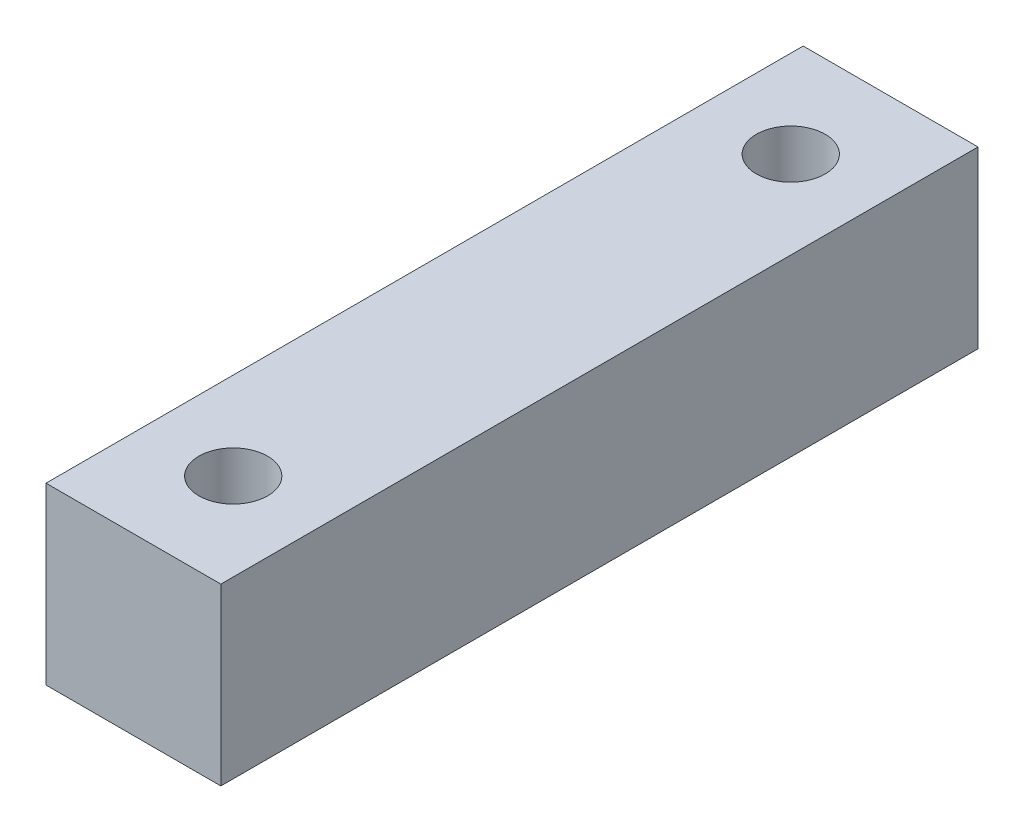
SolidWorks part; units mm, degrees
ref_plane "Front" through (0, 0, 0) normal (0, 0, 1) x (1, 0, 0)
ref_plane "Top" through (0, 0, 0) normal (0, 1, 0) x (1, 0, 0)
ref_plane "Right" through (0, 0, 0) normal (1, 0, 0) x (0, 0, -1)
sketch "Sketch1" plane through (0, 0, 0) normal (0, 1, 0) x (1, 0, 0)
  line L0 (0, 0) -> (0, 55)
  line L1 (0, 55) -> (12.7, 55)
  line L2 (12.7, 55) -> (12.7, 0)
  line L3 (12.7, 0) -> (0, 0)
  circle A0 centre (6.35, 7.25) radius 2.5
  circle A1 centre (6.35, 47.75) radius 2.5
  point P9 (6.35, 0)
  dimension "D3" = 5
  dimension "D4" = 7.25
  dimension "D1" = 12.7
  dimension "D2" = 55
  dimension "D5" = 7.25
  dimension "D6" = 6.35
extrude "Boss-Extrude1" add sketch "Sketch1" along normal blind 12.7
